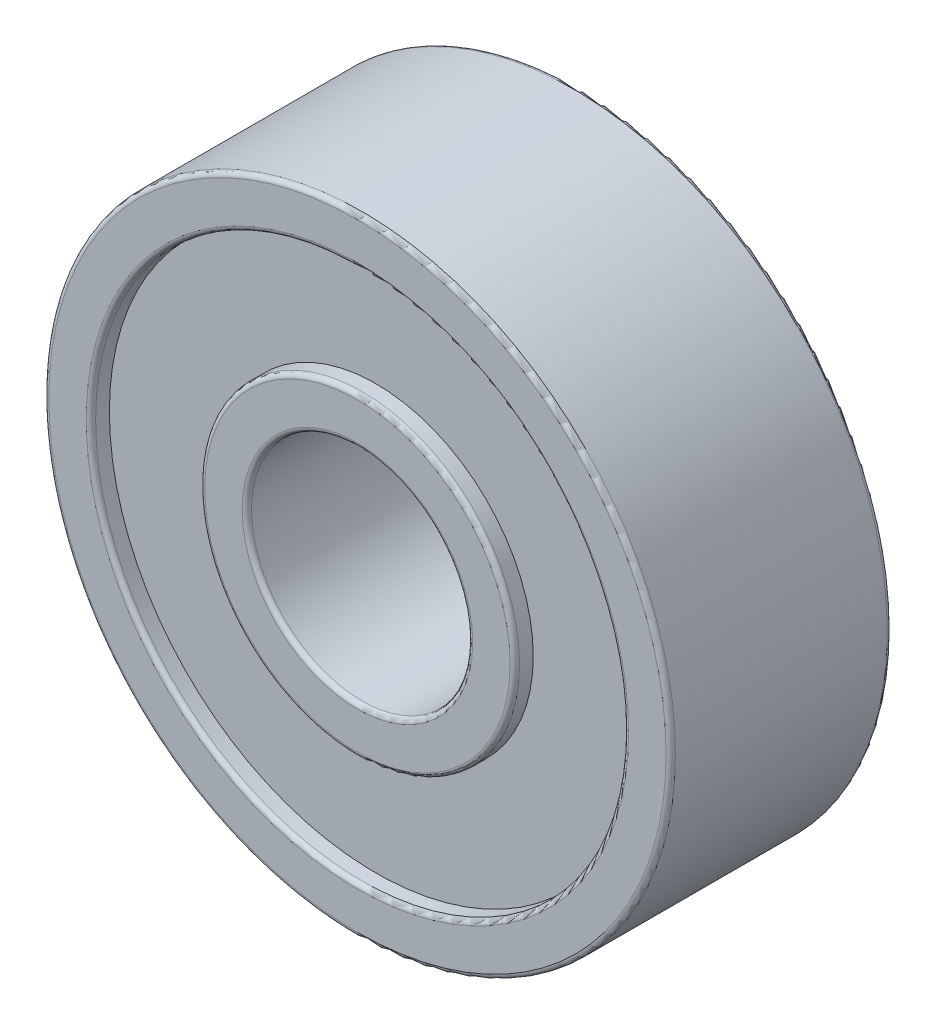
SolidWorks part; units mm, degrees
ref_plane "Front Plane" through (0, 0, 0) normal (0, 0, 1) x (1, 0, 0)
ref_plane "Top Plane" through (0, 0, 0) normal (0, 1, 0) x (1, 0, 0)
ref_plane "Right Plane" through (0, 0, 0) normal (1, 0, 0) x (0, 0, -1)
sketch "Sketch1" plane through (0, 0, 0) normal (0, 0, 1) x (1, 0, 0)
  circle A0 centre (0, 0) radius 4.27
  circle A1 centre (0, 0) radius 3
  dimension "D1" = 6
  dimension "D2" = 1.27
extrude "Boss-Extrude1" add sketch "Sketch1" along normal mid plane 6
sketch "Sketch2" plane through (0, 0, 0) normal (0, 0, 1) x (1, 0, 0)
  circle A0 centre (0, 0) radius 8.5
  circle A1 centre (0, 0) radius 7.23
  dimension "D1" = 17
  dimension "D2" = 1.27
extrude "Boss-Extrude2" add sketch "Sketch2" along normal mid plane 6 separate body
fillet "Fillet1" radius 0.127 4 edges at (7.23, 0, -3) (8.5, 0, -3) (7.23, 0, 3) (8.5, 0, 3)
fillet "Fillet2" radius 0.127 4 edges at (3, 0, -3) (4.27, 0, -3) (3, 0, 3) (4.27, 0, 3)
sketch "Sketch3" plane through (0, 0, 0) normal (0, 0, 1) x (1, 0, 0)
  circle A0 centre (0, 0) radius 7.23 construction
  circle A1 centre (0, 0) radius 4.27 construction
  circle A2 centre (0, 0) radius 7.23
  circle A3 centre (0, 0) radius 4.27
extrude "Boss-Extrude3" add sketch "Sketch3" along normal mid plane 5 separate body
